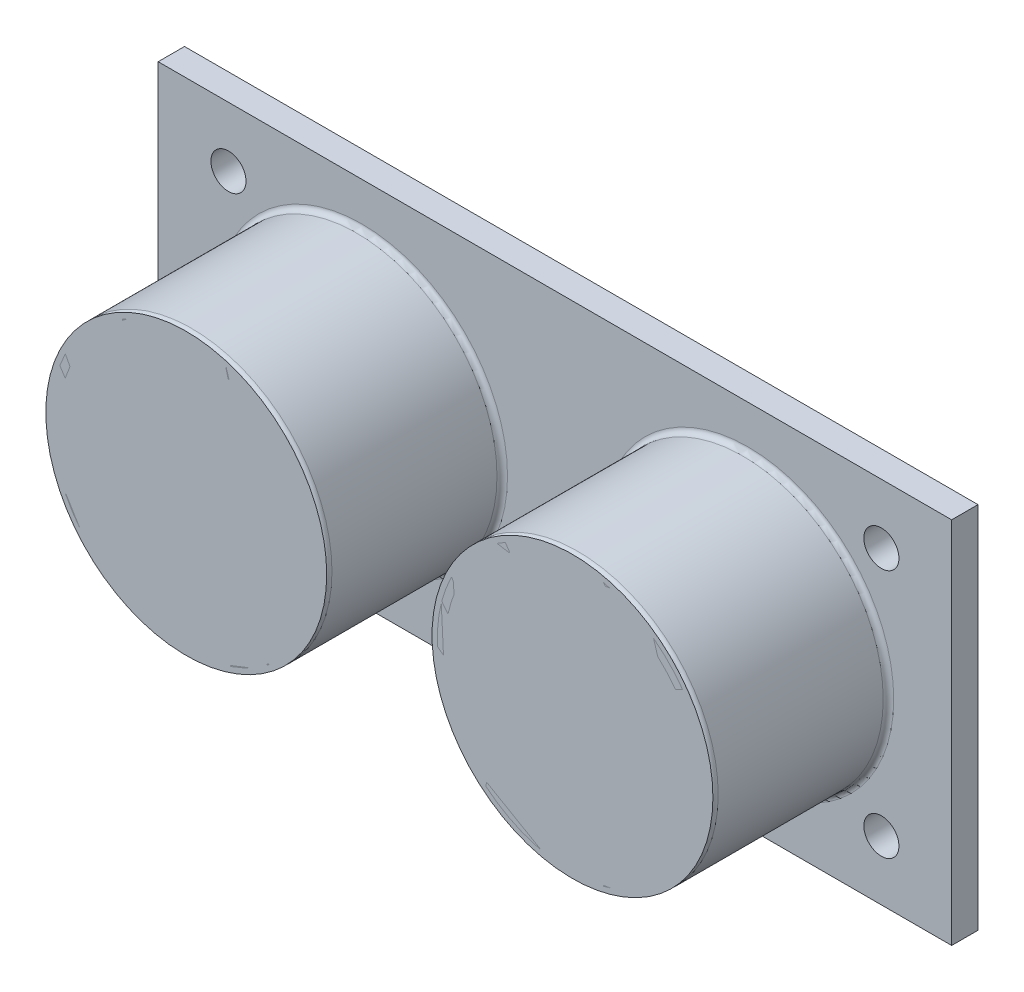
SolidWorks part; units mm, degrees
material "Alloy Steel"
ref_plane "Front Plane" through (0, 0, 0) normal (0, 0, 1) x (1, 0, 0)
ref_plane "Top Plane" through (0, 0, 0) normal (0, 1, 0) x (1, 0, 0)
ref_plane "Right Plane" through (0, 0, 0) normal (1, 0, 0) x (0, 0, -1)
sketch "Sketch1" plane through (0, 0, 0) normal (0, 0, 1) x (1, 0, 0)
  line L1 (-22.6, 10.5) -> (22.6, 10.5)
  line L2 (-22.6, 10.5) -> (-22.6, -10.5)
  line L3 (-22.6, -10.5) -> (22.6, -10.5)
  line L4 (22.6, 10.5) -> (22.6, -10.5)
  line L5 (-22.6, 10.5) -> (22.6, -10.5) construction
  line L6 (-22.6, -10.5) -> (22.6, 10.5) construction
  point P0 (0, 0)
  dimension "D1" = 45.2
  dimension "D2" = 21
extrude "Boss-Extrude1" add sketch "Sketch1" along normal mid plane 1.5
sketch "Sketch2" plane through (0, 0, 0.75) normal (0, 0, 1) x (1, 0, 0)
  line L1 (-22.6, 10.5) -> (-22.6, -10.5) construction
  circle A0 centre (-18.5965, 7.0992) radius 1
  dimension "D1" = 2
  dimension "D2" = 4.0035
extrude "Cut-Extrude1" cut sketch "Sketch2" against normal through all
mirror "Mirror1" about plane through (0, 0, 0) normal (1, 0, 0) of "Cut-Extrude1"
mirror "Mirror2" about plane through (0, 0, 0) normal (0, 1, 0) of "Mirror1", "Cut-Extrude1"
sketch "Sketch3" plane through (0, 0, 0.75) normal (0, 0, 1) x (1, 0, 0)
  circle A0 centre (-11, 0) radius 8
  dimension "D1" = 16
  dimension "D2" = 11
extrude "Boss-Extrude2" add sketch "Sketch3" along normal blind 10 contours A0
sketch "Sketch9" plane through (0, 0, 10.75) normal (0, 0, 1) x (1, 0, 0)
  circle A0 centre (-11, 0) radius 7.25
  dimension "D1" = 14.5
extrude "Cut-Extrude2" cut sketch "Sketch9" against normal blind 8
mirror "Mirror3" about plane through (0, 0, 0) normal (1, 0, 0) of "Boss-Extrude2"
mirror "Mirror4" about plane through (0, 0, 0) normal (1, 0, 0) of "Cut-Extrude2"
fillet "Fillet1" radius 0.3 4 edges at (3, 0, 10.75) (19, 0, 0.75) (-3, 0, 10.75) (-3, 0, 0.75)
sketch "Sketch10" plane through (0, 0, 2.75) normal (0, 0, 1) x (1, 0, 0)
  circle A0 centre (-11, 0) radius 5.6
extrude "Boss-Extrude3" add sketch "Sketch10" along normal blind 4
mirror "Mirror5" about plane through (0, 0, 0) normal (1, 0, 0) of "Boss-Extrude3"
sketch "Sketch12" plane through (0, 0, 10.75) normal (0, 0, 1) x (1, 0, 0)
  circle A0 centre (-11, 0) radius 8
surface "Surface-Fill1" sketch "Sketch12"
sketch "Sketch14" plane through (0, 0, 10.75) normal (0, 0, 1) x (1, 0, 0)
  circle A0 centre (11, 0) radius 8
surface "Surface-Fill2" sketch "Sketch14"
ref_point "Point1"
